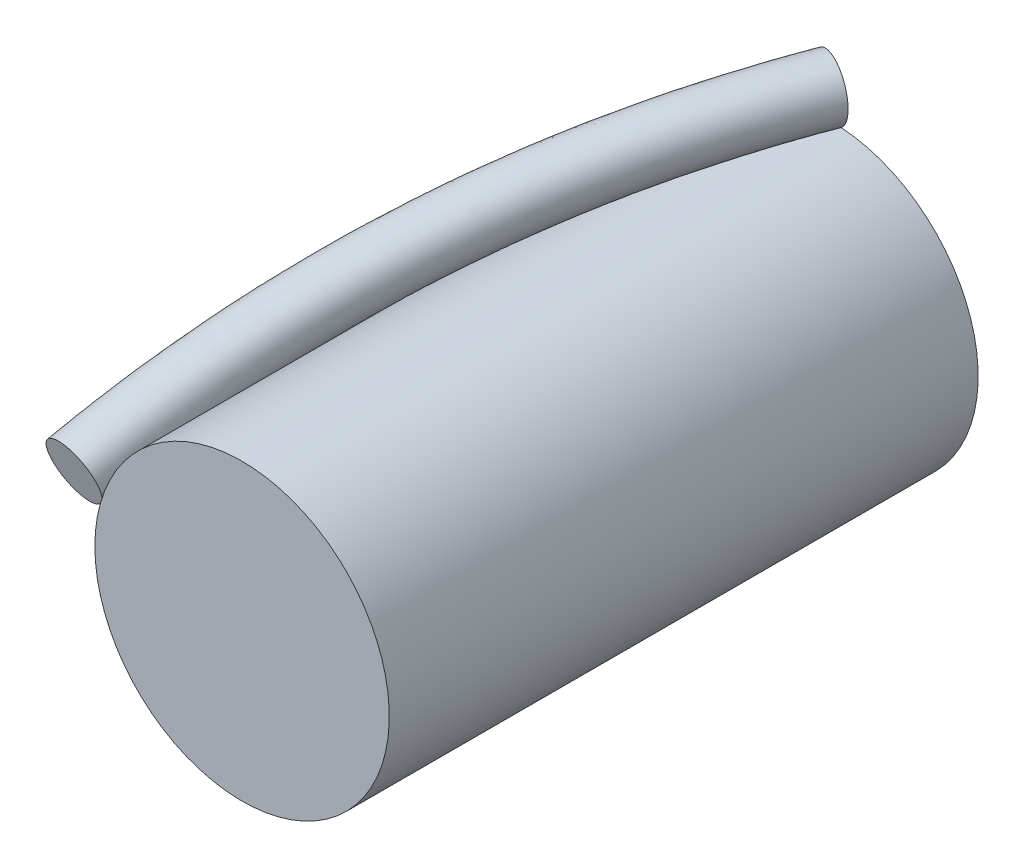
SolidWorks part; units mm, degrees
ref_plane "Ebene vorne" through (0, 0, 0) normal (0, 0, 1) x (1, 0, 0)
ref_plane "Ebene oben" through (0, 0, 0) normal (0, 1, 0) x (1, 0, 0)
ref_plane "Ebene rechts" through (0, 0, 0) normal (1, 0, 0) x (0, 0, -1)
sketch "Skizze1" plane through (0, 0, 0) normal (1, 0, 0) x (0, 0, -1)
  line L0 (0, 0) -> (-101.105, 0) construction
  line L2 (-100, 0) -> (0, 0)
  line L3 (-100, 0) -> (-100, 25)
  line L4 (-100, 25) -> (0, 25)
  line L5 (0, 0) -> (0, 25)
  dimension "D1" = 50
  dimension "D2" = 100
revolve "Rotation1" add sketch "Skizze1" angle 360 about L0
sketch "Skizze3" plane through (0, 0, 0) normal (0, 0, -1) x (-1, 0, 0)
  circle A2 centre (0, 0) radius 30
  circle A3 centre (0, 0) radius 30
  dimension "D1" = 5
curve "Spirale/Helix1" pitch 500 height 100 turns 0.2
ref_plane "Ebene1" through (0, 30, 0) normal (-0.3528, 0, 0.9357) x (0.9357, 0, 0.3528)
sketch "Skizze4" plane through (0, 30, 0) normal (-0.3528, 0, 0.9357) x (0.9357, 0, 0.3528)
  line L0 (35.2756, -30) -> (0, -30) construction
  circle A0 centre (0, 0) radius 5
  dimension "D2" = 10
  dimension "D1" = 30
sweep "Austragung1" add profiles "Skizze4" path "Spirale/Helix1"
